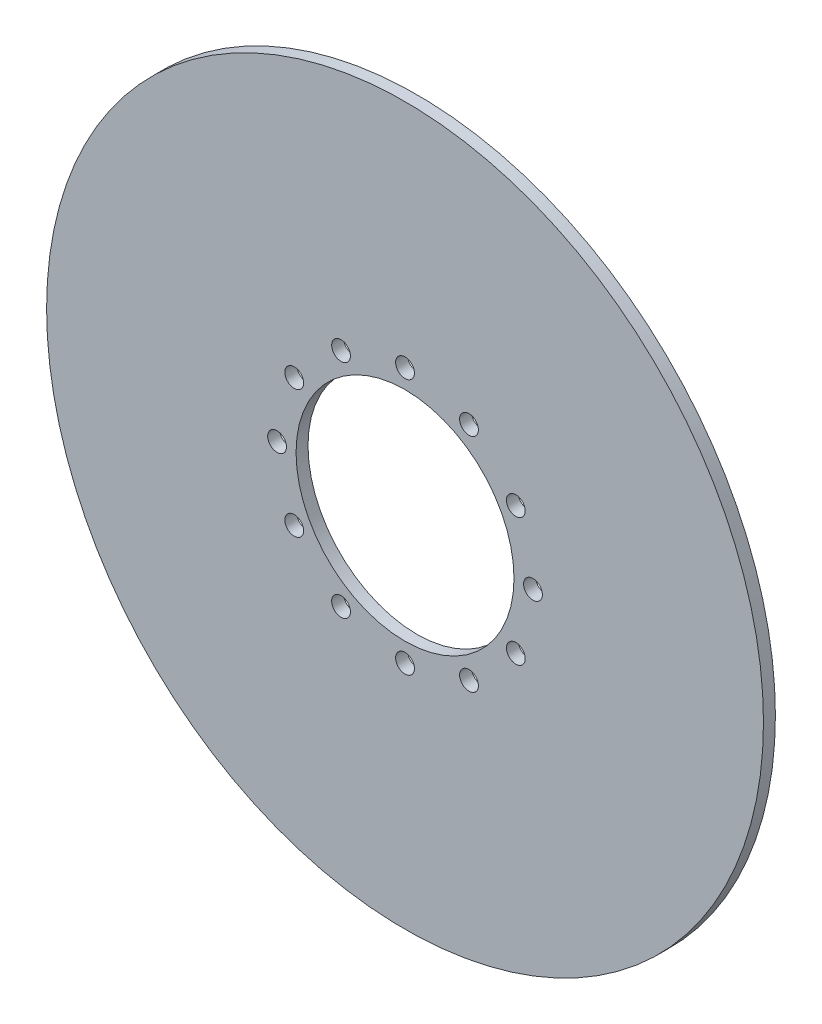
SolidWorks part; units mm, degrees
material "AISI 1020"
ref_plane "Front Plane" through (0, 0, 0) normal (0, 0, 1) x (1, 0, 0)
ref_plane "Top Plane" through (0, 0, 0) normal (0, 1, 0) x (1, 0, 0)
ref_plane "Right Plane" through (0, 0, 0) normal (1, 0, 0) x (0, 0, -1)
sketch "Sketch1" plane through (0, 0, 0) normal (0, 0, 1) x (1, 0, 0)
  circle A0 centre (0, 0) radius 95.25
  circle A1 centre (0, 0) radius 28.956
  circle A2 centre (0, 0) radius 34 construction
  circle A3 centre (0, 34) radius 2.497
  circle A4 centre (17, 29.4449) radius 2.497
  circle A5 centre (29.4449, 17) radius 2.497
  circle A6 centre (34, 0) radius 2.497
  circle A7 centre (29.4449, -17) radius 2.497
  circle A8 centre (17, -29.4449) radius 2.497
  circle A9 centre (0, -34) radius 2.497
  circle A10 centre (-17, -29.4449) radius 2.497
  circle A11 centre (-29.4449, -17) radius 2.497
  circle A12 centre (-34, 0) radius 2.497
  circle A13 centre (-29.4449, 17) radius 2.497
  circle A14 centre (-17, 29.4449) radius 2.497
  point P32 (0, 0)
  dimension "D1" = 190.5
  dimension "D2" = 57.912
  dimension "D3" = 68
  dimension "D4" = 12
extrude "Boss-Extrude1" add sketch "Sketch1" along normal blind 3.175
move or copy body "Body-Move/Copy2" [suppressed] bodies to move or copy 101
move or copy body "Body-Move/Copy1" [suppressed] bodies to move or copy 101
